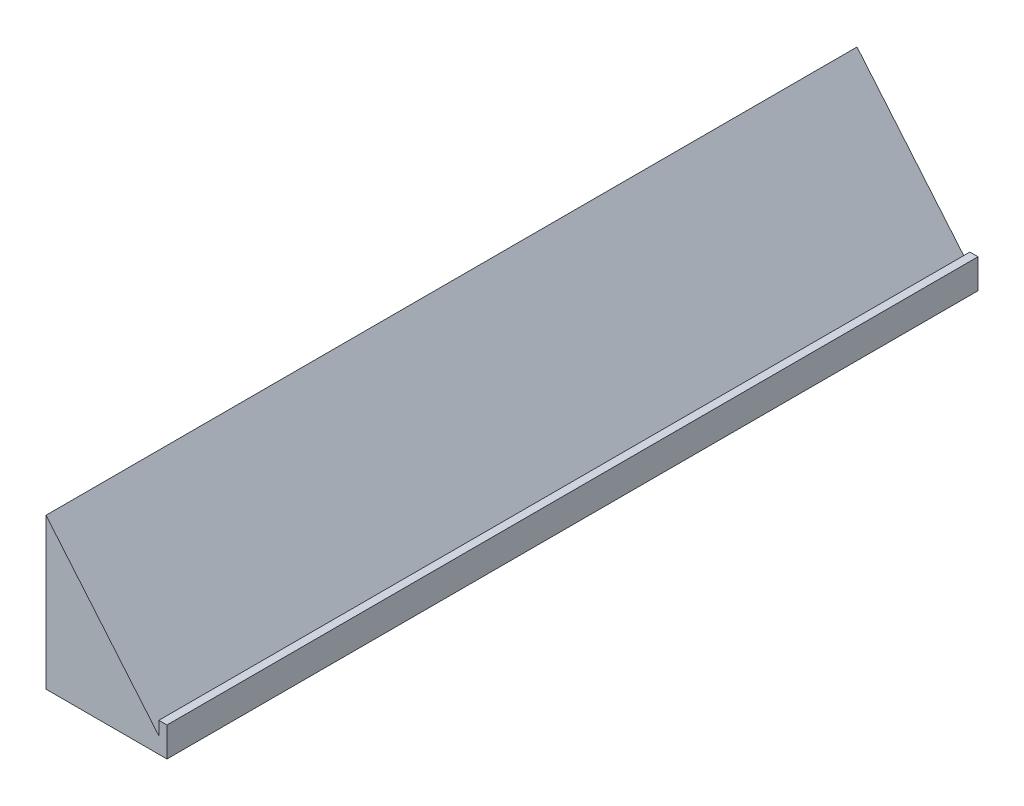
SolidWorks part; units mm, degrees
ref_plane "Front Plane" through (0, 0, 0) normal (0, 0, 1) x (1, 0, 0)
ref_plane "Top Plane" through (0, 0, 0) normal (0, 1, 0) x (1, 0, 0)
ref_plane "Right Plane" through (0, 0, 0) normal (1, 0, 0) x (0, 0, -1)
sketch "Sketch3" plane through (0, 0, 0) normal (0, 0, 1) x (1, 0, 0)
  line L0 (0, 0) -> (0, 50)
  line L1 (0, 50) -> (41.7471, 0.1785)
  line L2 (41.7471, 0.1785) -> (41.7471, 5.1785)
  line L3 (41.7471, 5.1785) -> (44.7471, 5.1785)
  line L4 (44.7471, 5.1785) -> (44.7471, -5.7282)
  line L5 (44.7471, -5.7282) -> (0, -5.7282)
  line L6 (0, -5.7282) -> (0, 0)
  dimension "D1" = 50
  dimension "D2" = 65
  dimension "D3" = 5
  dimension "D4" = 3
extrude "Boss-Extrude1" add sketch "Sketch3" along normal blind 300
